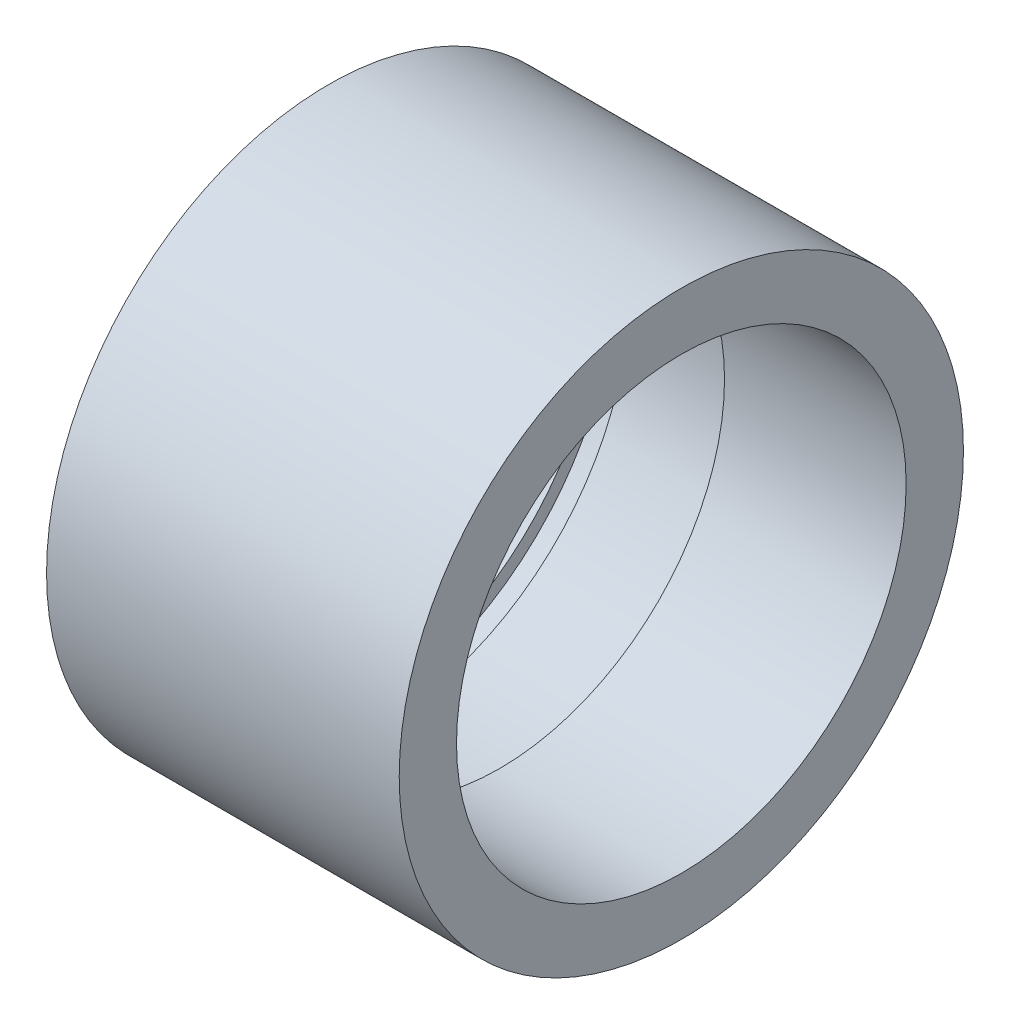
SolidWorks part; units mm, degrees
material "AISI 1020"
ref_plane "Спереди" through (0, 0, 0) normal (0, 0, 1) x (1, 0, 0)
ref_plane "Сверху" through (0, 0, 0) normal (0, 1, 0) x (1, 0, 0)
ref_plane "Справа" through (0, 0, 0) normal (1, 0, 0) x (0, 0, -1)
sketch "Эскиз1" plane through (0, 0, 0) normal (0, 1, 0) x (1, 0, 0)
  line L0 (-1000, 0) -> (49000, 0) construction
  line L1 (-1.5, 14) -> (0, 14)
  line L2 (0, 14.75) -> (0, -14.75) construction
  line L3 (0, 14) -> (0, 14.75)
  line L4 (0, 14.75) -> (1.5, 14.75)
  line L5 (1.5, 14.75) -> (1.5, 14)
  line L6 (7.7, 14) -> (1.7, 14) construction
  line L7 (1.5, 14) -> (8.2, 14)
  line L8 (8.2, 14) -> (8.2, 12.75)
  line L9 (8.2, 12.75) -> (18.5, 12.75)
  line L10 (18.5, 12.75) -> (18.5, 16)
  line L11 (18.5, 16) -> (-1.5, 16)
  line L12 (-1.5, 16) -> (-1.5, 14)
  line L13 (8.2, -13.5) -> (8.2, 13.5) construction
  line L14 (0, 14.75) -> (-0.75, 14) construction
  line L15 (-0.75, 14) -> (-1.5, 14.75) construction
  dimension "D1" = 25.5
  dimension "D2" = 45
  dimension "D3" = 1.5
  dimension "D4" = 32
  dimension "D5" = 20
revolve "Повернуть1" add sketch "Эскиз1" angle 360 about L0
sketch "Эскиз2" [suppressed] plane through (0, 0, 0) normal (0, 0, 1) x (1, 0, 0)
  line L0 (-1000, 0) -> (49000, 0) construction
  line L3 (18.5, 12.75) -> (8.2, 12.75) construction
  line L4 (18.5, 12.75) -> (8.2, 12.75)
  line L5 (8.2, 12.75) -> (7.9, 12.75)
  line L6 (7.9, 12.75) -> (7.9, 14.75)
  line L7 (7.9, 14.75) -> (9.4, 14.75)
  line L8 (9.4, 14.75) -> (9.4, 14)
  line L9 (9.4, 14) -> (18.5, 14)
  line L10 (18.5, -16) -> (18.5, 16) construction
  line L11 (18.5, 14) -> (18.5, 12.75)
  line L12 (1.5, 14.75) -> (0, 14.75) construction
  line L13 (8.2, 14) -> (1.5, 14) construction
  dimension "D1" = 0.3
revolve "Вырез-Повернуть1" [suppressed] cut sketch "Эскиз2" angle 360 about L0
